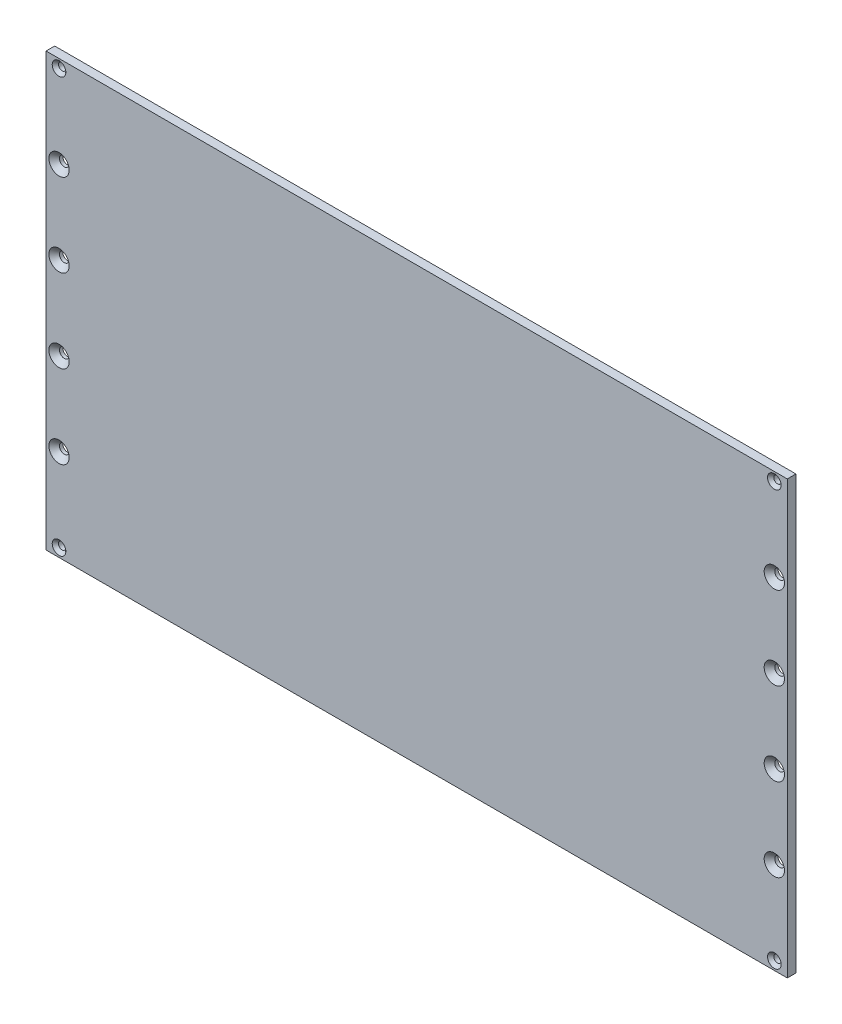
SolidWorks part; units mm, degrees
ref_plane "Front Plane" through (0, 0, 0) normal (0, 0, 1) x (1, 0, 0)
ref_plane "Top Plane" through (0, 0, 0) normal (0, 1, 0) x (1, 0, 0)
ref_plane "Right Plane" through (0, 0, 0) normal (1, 0, 0) x (0, 0, -1)
sketch "Sketch1" plane through (0, 0, 0) normal (0, 0, 1) x (1, 0, 0)
  line L1 (0, 0) -> (343, 0)
  line L2 (0, 0) -> (0, 200)
  line L3 (0, 200) -> (343, 200)
  line L4 (343, 0) -> (343, 200)
extrude "Extrude1" add sketch "Sketch1" along normal blind 4
sketch "Sketch2" plane through (0, 0, 4) normal (0, 0, 1) x (1, 0, 0)
  line L0 (6, 0) -> (6, 200) construction
  line L1 (0, 0) -> (343, 0) construction
  line L2 (343, 200) -> (0, 200) construction
  line L3 (337, 200) -> (337, 0) construction
  point P6 (6, 4)
  point P7 (6, 196)
  point P10 (337, 196)
  point P11 (337, 4)
  point P12 (6, 42.4)
  point P13 (337, 42.4)
hole_wizard "CSK for M3 Countersunk Flat Head Screw1" positions "3DSketch1" profile "Sketch3" countersink size "M3" standard "DIN" end condition through all
sketch3d "3DSketch1"
  point P0 (6, 196, 4)
  point P3 (6, 4, 4)
  point P6 (337, 4, 4)
  point P9 (337, 196, 4)
sketch "Sketch3" plane through (6, 196, 4) normal (1, 0, 0) x (0, -1, 0)
  line L0 (0, 0) -> (0, 4)
  line L1 (0, 4) -> (1.7, 4)
  line L2 (1.7, 4) -> (1.7, 1.45)
  line L3 (1.7, 1.45) -> (3.15, 0)
  line L5 (3.15, 0) -> (0, 0)
  line L6 (-1.7, 1.45) -> (-3.15, 0) construction
  line L11 (0, -6.35) -> (0, 107.95) construction
  dimension "Thru Hole Dia." = 3.4
  dimension "Thru Hole Depth" = 4
  dimension "Near C'Sink Dia." = 6.3
  dimension "Near C'Sink Angle" = 90
hole_wizard "CSK for M4 Countersunk Flat Head Screw1" positions "3DSketch2" profile "Sketch4" countersink size "M4" standard "DIN" end condition through all
sketch3d "3DSketch2"
  point P0 (6, 42.4, 4)
  point P3 (337, 42.4, 4)
sketch "Sketch4" plane through (6, 42.4, 4) normal (1, 0, 0) x (0, -1, 0)
  line L0 (0, 0) -> (0, 4)
  line L1 (0, 4) -> (2.25, 4)
  line L2 (2.25, 4) -> (2.25, 2.45)
  line L3 (2.25, 2.45) -> (4.7, 0)
  line L5 (4.7, 0) -> (0, 0)
  line L6 (-2.25, 2.45) -> (-4.7, 0) construction
  line L11 (0, -6.35) -> (0, 107.95) construction
  dimension "Thru Hole Dia." = 4.5
  dimension "Thru Hole Depth" = 4
  dimension "Near C'Sink Dia." = 9.4
  dimension "Near C'Sink Angle" = 90
pattern_linear "LPattern1" count 4 spacing 38.4 along (0, 1, 0) of "CSK for M4 Countersunk Flat Head Screw1"
